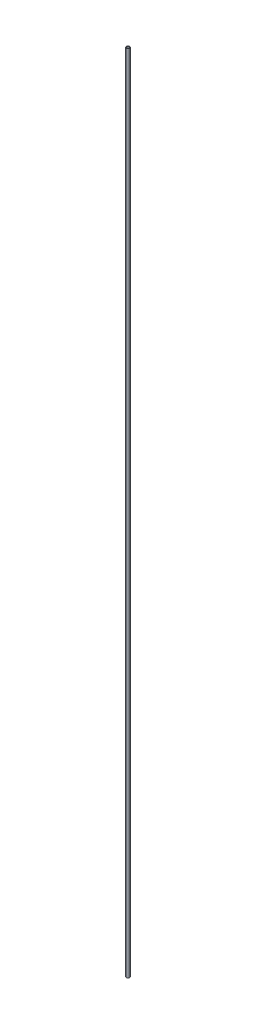
SolidWorks part; units mm, degrees
material "Hexcel AS4C (3000 Filaments)"
ref_plane "Front Plane" through (0, 0, 0) normal (0, 0, 1) x (1, 0, 0)
ref_plane "Top Plane" through (0, 0, 0) normal (0, 1, 0) x (1, 0, 0)
ref_plane "Right Plane" through (0, 0, 0) normal (1, 0, 0) x (0, 0, -1)
sketch "Sketch1" plane through (0, 0, 0) normal (0, 1, 0) x (1, 0, 0)
  circle A0 centre (0, 0) radius 2
  circle A1 centre (0, 0) radius 1.5
  dimension "D1" = 4
  dimension "D2" = 3
extrude "Boss-Extrude1" add sketch "Sketch1" along normal blind 1000
